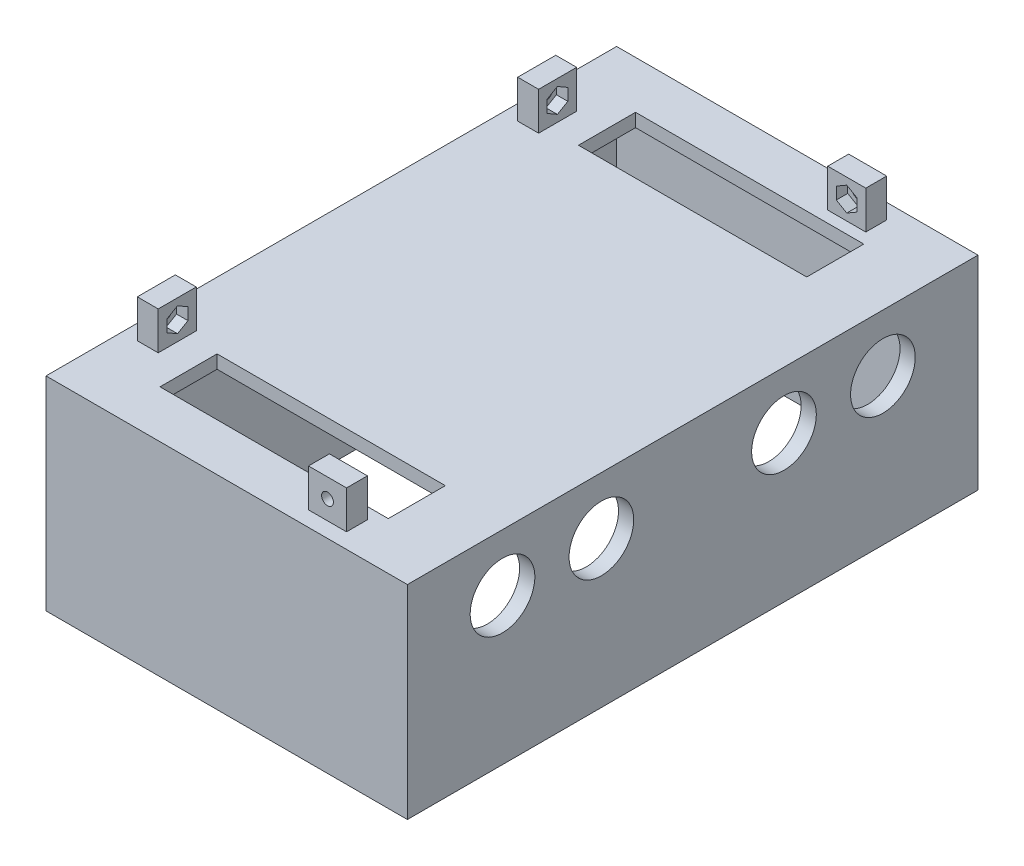
SolidWorks part; units mm, degrees
ref_plane "Front" through (0, 0, 0) normal (0, 0, 1) x (1, 0, 0)
ref_plane "Top" through (0, 0, 0) normal (0, 1, 0) x (1, 0, 0)
ref_plane "Right" through (0, 0, 0) normal (1, 0, 0) x (0, 0, -1)
sketch "Sketch1" plane through (0, 0, 0) normal (0, 1, 0) x (1, 0, 0)
  line L1 (47.5, -75) -> (-47.5, -75)
  line L2 (47.5, -75) -> (47.5, 75)
  line L3 (47.5, 75) -> (-47.5, 75)
  line L4 (-47.5, -75) -> (-47.5, 75)
  line L5 (0, 75) -> (0, -75) construction
  line L6 (47.5, 0) -> (-47.5, 0) construction
  point P0 (0, 0)
  dimension "D1" = 95
  dimension "D2" = 150
extrude "Boss-Extrude1" add sketch "Sketch1" along normal blind 3.5
sketch "Sketch2" plane through (0, 3.5, 0) normal (0, 1, 0) x (1, 0, 0)
  line L0 (-43.5, 55) -> (-38, 55)
  line L1 (43.5, -71) -> (-43.5, -71) construction
  line L2 (43.5, -71) -> (43.5, 71) construction
  line L3 (43.5, 71) -> (-43.5, 71) construction
  line L4 (-43.5, -71) -> (-43.5, 71) construction
  line L5 (0, 71) -> (0, -71) construction
  line L6 (43.5, 0) -> (-43.5, 0) construction
  line L7 (-38, 55) -> (-38, 45)
  line L8 (-38, 45) -> (-43.5, 45)
  line L9 (47.5, 75) -> (-47.5, 75) construction
  line L10 (27.5, 71) -> (27.5, 65.5)
  line L11 (27.5, 65.5) -> (17.5, 65.5)
  line L12 (17.5, 65.5) -> (17.5, 71)
  line L13 (47.5, -75) -> (47.5, 75) construction
  line L14 (-43.5, 55) -> (-43.5, 45)
  line L15 (17.5, 71) -> (27.5, 71)
  point P0 (0, 0)
  dimension "D1" = 87
  dimension "D2" = 142
  dimension "D3" = 20
  dimension "D4" = 10
  dimension "D5" = 5.5
  dimension "D6" = 20
  dimension "D7" = 10
  dimension "D8" = 5.5
extrude "Boss-Extrude2" add sketch "Sketch2" along normal blind 10
sketch "Sketch3" plane through (0, 0, -65.5) normal (0, 0, 1) x (1, 0, 0)
  line L6 (22.5, 5.3246) -> (25.25, 6.9123)
  line L7 (25.25, 6.9123) -> (25.25, 10.0877)
  line L8 (25.25, 10.0877) -> (22.5, 11.6754)
  line L9 (22.5, 11.6754) -> (19.75, 10.0877)
  line L10 (19.75, 10.0877) -> (19.75, 6.9123)
  line L11 (19.75, 6.9123) -> (22.5, 5.3246)
  circle A0 centre (22.5, 8.5) radius 2.75 construction
extrude "Cut-Extrude1" cut sketch "Sketch3" against normal blind 3
sketch "Sketch4" plane through (-38, 0, 0) normal (1, 0, 0) x (0, 0, -1)
  line L4 (49.9281, 5.3246) -> (52.6781, 6.9123)
  line L5 (52.6781, 6.9123) -> (52.6781, 10.0877)
  line L6 (52.6781, 10.0877) -> (49.9281, 11.6754)
  line L7 (49.9281, 11.6754) -> (47.1781, 10.0877)
  line L8 (47.1781, 10.0877) -> (47.1781, 6.9123)
  line L9 (47.1781, 6.9123) -> (49.9281, 5.3246)
  circle A0 centre (49.9281, 8.5) radius 2.75 construction
extrude "Cut-Extrude2" cut sketch "Sketch4" against normal blind 3
sketch "Sketch6" plane through (-38, 0, 0) normal (1, 0, 0) x (0, 0, -1)
  circle A0 centre (50, 8.5) radius 1.55
extrude "Cut-Extrude3" cut sketch "Sketch6" against normal through all contours A0
sketch "Sketch7" plane through (0, 0, -65.5) normal (0, 0, 1) x (1, 0, 0)
  circle A0 centre (22.5, 8.5) radius 1.55
extrude "Cut-Extrude4" cut sketch "Sketch7" against normal through all
sketch "Sketch8" plane through (0, 0, 0) normal (0, -1, 0) x (1, 0, 0)
  line L1 (-43.5, 71) -> (43.5, 71)
  line L2 (-43.5, 71) -> (-43.5, -71)
  line L3 (-43.5, -71) -> (43.5, -71)
  line L4 (43.5, 71) -> (43.5, -71)
  line L5 (0, -71) -> (0, 71) construction
  line L6 (-43.5, 0) -> (43.5, 0) construction
  line L7 (-47.5, 75) -> (47.5, 75)
  line L8 (-47.5, 75) -> (-47.5, -75)
  line L9 (-47.5, -75) -> (47.5, -75)
  line L10 (47.5, 75) -> (47.5, -75)
  line L11 (0, -75) -> (0, 75) construction
  line L12 (-47.5, 0) -> (47.5, 0) construction
  point P0 (0, 0)
  point P4 (0, 0)
  dimension "D1" = 87
  dimension "D2" = 142
extrude "Boss-Extrude3" add sketch "Sketch8" along normal blind 50
sketch "Sketch9" plane through (0, 0, 0) normal (0, -1, 0) x (1, 0, 0)
  line L0 (-47.5, -75) -> (47.5, -75) construction
  line L1 (-30.0269, -62.5) -> (29.9731, -62.5)
  line L2 (-30.0269, -62.5) -> (-30.0269, -47.5)
  line L3 (-30.0269, -47.5) -> (29.9731, -47.5)
  line L4 (29.9731, -62.5) -> (29.9731, -47.5)
  line L5 (-0.0269, -47.5) -> (-0.0269, -62.5) construction
  line L6 (-30.0269, -55) -> (29.9731, -55) construction
  point P0 (-0.0269, -55)
  dimension "D1" = 60
  dimension "D2" = 15
  dimension "D3" = 20
extrude "Cut-Extrude5" cut sketch "Sketch9" against normal blind 50
sketch "Sketch10" plane through (47.5, 0, 0) normal (1, 0, 0) x (0, 0, -1)
  line L0 (75, 3.5) -> (75, -50) construction
  line L1 (-75, 3.5) -> (75, 3.5) construction
  circle A0 centre (50, -11.5) radius 8.5
  circle A1 centre (24, -11.5) radius 8.5
  dimension "D1" = 26
  dimension "D2" = 25
  dimension "D3" = 15
extrude "Cut-Extrude6" cut sketch "Sketch10" against normal blind 50
mirror "Mirror1" about plane through (0, 0, 0) normal (0, 0, 1) of "Cut-Extrude5", "Cut-Extrude1", "Cut-Extrude2", "Boss-Extrude2", "Cut-Extrude6", "Cut-Extrude4", "Cut-Extrude3"
ref_plane "Plane1" through (-41, 0, 0) normal (1, 0, 0) x (0, 0, -1)
